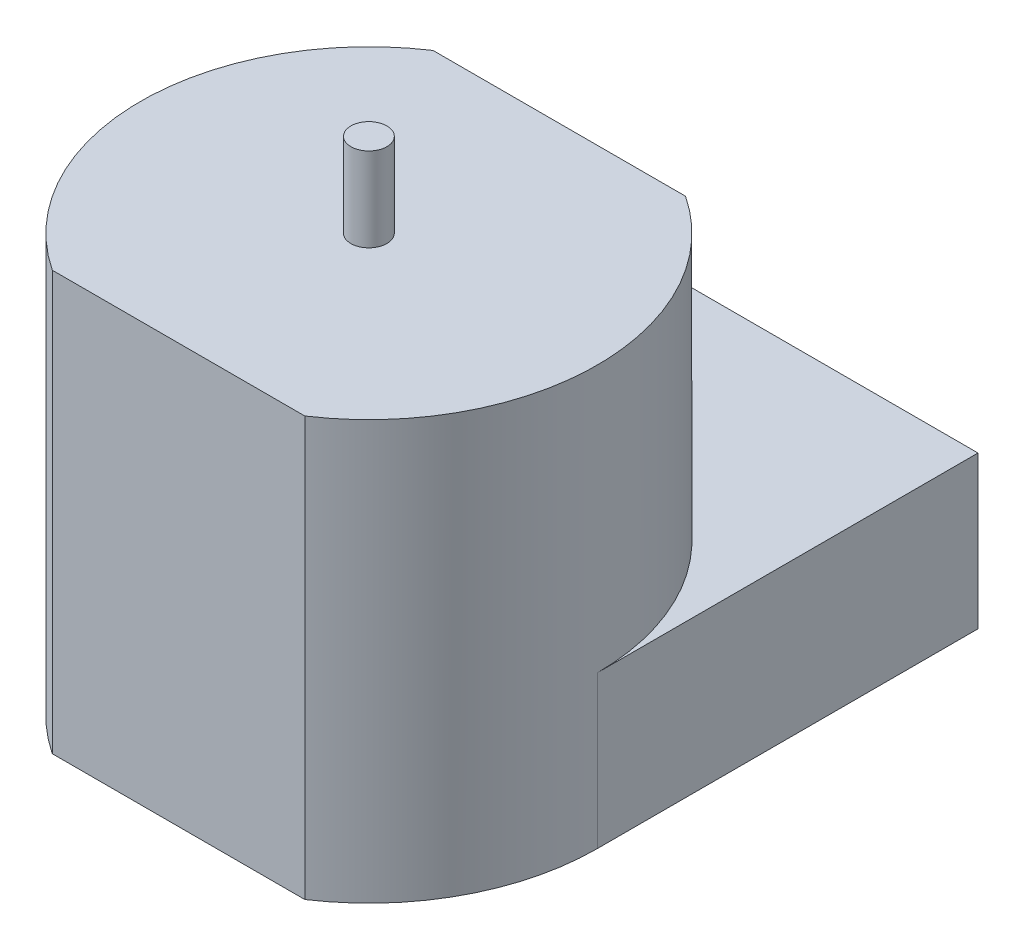
SolidWorks part; units mm, degrees
ref_plane "Front Plane" through (0, 0, 0) normal (0, 0, 1) x (1, 0, 0)
ref_plane "Top Plane" through (0, 0, 0) normal (0, 1, 0) x (1, 0, 0)
ref_plane "Right Plane" through (0, 0, 0) normal (1, 0, 0) x (0, 0, -1)
sketch "Sketch1" plane through (0, 0, 0) normal (0, 1, 0) x (1, 0, 0)
  line L1 (-5.2651, 7.9375) -> (5.2651, 7.9375)
  line L2 (-5.2651, 7.9375) -> (-5.2651, -7.9375)
  line L3 (-5.2651, -7.9375) -> (5.2651, -7.9375)
  line L4 (5.2651, 7.9375) -> (5.2651, -7.9375)
  line L5 (-5.2651, 7.9375) -> (5.2651, -7.9375) construction
  line L6 (-5.2651, -7.9375) -> (5.2651, 7.9375) construction
  line L7 (9.525, 0) -> (-9.525, 0)
  line L8 (9.525, 0) -> (9.525, 15.875)
  line L9 (9.525, 15.875) -> (-9.525, 15.875)
  line L10 (-9.525, 0) -> (-9.525, 15.875)
  circle A0 centre (0, 0) radius 9.525
  dimension "D1" = 19.05
  dimension "D2" = 15.875
  dimension "D3" = 23.8125
  dimension "D4" = 19.05
extrude "Boss-Extrude1" add sketch "Sketch1" along normal blind 6.35 contours L7 A0 L2 | L4 L7 L2 L3 | L4 A0 L7 | L7 A0 L4 | A0 L8 L9 L10 | L7 L4 L1 L2 | L1 A0 | L2 A0 L7
sketch "Sketch2" plane through (0, 6.35, 0) normal (0, 1, 0) x (1, 0, 0)
  line L1 (-5.2651, 7.9375) -> (5.2651, 7.9375)
  line L2 (-5.2651, 7.9375) -> (-5.2651, -7.9375)
  line L3 (-5.2651, -7.9375) -> (5.2651, -7.9375)
  line L4 (5.2651, 7.9375) -> (5.2651, -7.9375)
  line L5 (-5.2651, 7.9375) -> (5.2651, -7.9375) construction
  line L6 (-5.2651, -7.9375) -> (5.2651, 7.9375) construction
  circle A0 centre (0, 0) radius 9.525
  line M2 (-5.2651, -7.9375) -> (5.2651, -7.9375)
  arc M3 (5.2651, -7.9375) -> (9.525, 0) centre (0, 0) ccw
  arc M7 (-9.525, 0) -> (-5.2651, -7.9375) centre (0, 0) ccw
extrude "Boss-Extrude2" add sketch "Sketch2" along normal blind 11.1125 contours L2 A0 M7 | L4 L1 L2 M2 | A0 L4 M3
sketch "Sketch3" plane through (0, 17.4625, 0) normal (0, 1, 0) x (1, 0, 0)
  circle A0 centre (0, 0) radius 0.75
  dimension "D1" = 1.5
extrude "Boss-Extrude3" add sketch "Sketch3" along normal blind 3.5
